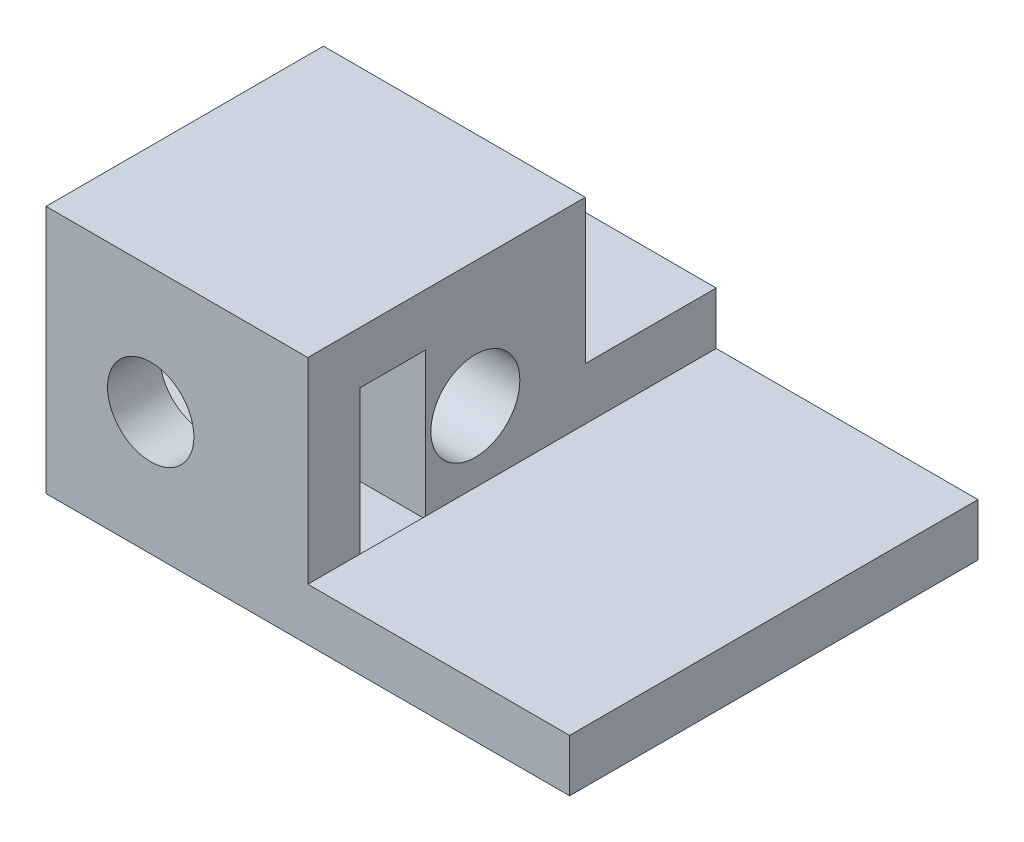
SolidWorks part; units mm, degrees
ref_plane "Plano frontal" through (0, 0, 0) normal (0, 0, 1) x (1, 0, 0)
ref_plane "Plano superior" through (0, 0, 0) normal (0, 1, 0) x (1, 0, 0)
ref_plane "Plano direito" through (0, 0, 0) normal (1, 0, 0) x (0, 0, -1)
sketch "Esboço1" plane through (0, 0, 0) normal (0, 0, 1) x (1, 0, 0)
  line L0 (0, 0) -> (0, 2)
  line L1 (0, 2) -> (5, 2)
  line L2 (5, 2) -> (5, 4)
  line L3 (5, 4) -> (10, 4)
  line L4 (10, 4) -> (10, 2)
  line L5 (20, 0) -> (0, 0)
  line L6 (10, 2) -> (20, 2)
  line L7 (20, 2) -> (20, 0)
  dimension "D1" = 2
  dimension "D2" = 2
  dimension "D3" = 5
  dimension "D4" = 5
  dimension "D5" = 10
extrude "Ressalto-extrusão1" add sketch "Esboço1" along normal mid plane 105
sketch "Esboço3" plane through (0, 0, 52.5) normal (0, 0, 1) x (1, 0, 0)
  line L1 (0, 0) -> (10, 0)
  line L2 (0, 0) -> (0, 4)
  line L3 (0, 4) -> (10, 4)
  line L4 (10, 0) -> (10, 4)
extrude "Ressalto-extrusão2" add sketch "Esboço3" against normal blind 5
sketch "Esboço4" plane through (10, 0, 0) normal (1, 0, 0) x (0, 0, -1)
  line L0 (-52.5, 9.5) -> (-63.1, 9.5)
  line L1 (-52.5, 9.5) -> (-52.5, 3.7429)
  line L2 (-63.1, 0) -> (-52.5, 0)
  line L4 (2.5, 0) -> (2.5, 21.5057) construction
  line L5 (-47.5, 0) -> (52.5, 0) construction
  line L6 (-63.1, 9.5) -> (-63.1, 0)
  line L8 (-61.1, 7.5) -> (-58.6, 7.5)
  line L9 (-52.5, 3.7429) -> (-52.5, 0)
  line L10 (-61.1, 7.5) -> (-61.1, 1.9)
  line L11 (-61.1, 1.9) -> (-58.6, 1.9)
  line L12 (-58.6, 7.5) -> (-58.6, 1.9)
  line L13 (-61.1, 7.5) -> (-58.6, 1.9) construction
  line L14 (-61.1, 1.9) -> (-58.6, 7.5) construction
  circle A0 centre (-56.7, 4.7) radius 1.7
  point P0 (-105, 0)
  point P4 (0, 0)
  point P7 (-106.4656, 8.3439)
  point P14 (-59.85, 4.7)
  point P22 (-116.5265, 8.4)
  point P23 (-109.0163, 8.4)
  point P24 (-115, 3.8609)
  dimension "D1" = 3.4
  dimension "D2" = 2
  dimension "D3" = 2.5
  dimension "D4" = 3
  dimension "D5" = 0.2
  dimension "D6" = 5.6
  dimension "D7" = 2.5
  dimension "D8" = 2
extrude "Ressalto-extrusão3" add sketch "Esboço4" against normal through all
sketch "Esboço5" plane through (0, 0, 63.1) normal (0, 0, 1) x (1, 0, 0)
  line L0 (0, 7.5) -> (0, 1.9) construction
  line L1 (0, 7.5) -> (0, 1.9) construction
  circle A0 centre (4, 4.7) radius 1.65
  point P4 (0, 4.7)
  point P5 (0, 0)
  dimension "D2" = 3.3
  dimension "D1" = 4
extrude "Corte-extrusão1" cut sketch "Esboço5" against normal blind 6
mirror "Espelhar1" about plane through (0, 0, 0) normal (0, 0, 1) of "Corte-extrusão1", "Ressalto-extrusão3"
sketch "Esboço6" plane through (0, 0, 52.5) normal (0, 0, 1) x (1, 0, 0)
  line L4 (10, 2) -> (10, 0)
  line L5 (10, 0) -> (20, 0)
  line L6 (20, 0) -> (20, 2)
  line L7 (20, 2) -> (10, 2)
  line L8 (10, 2) -> (10, 0)
  line L9 (10, 0) -> (20, 0)
  line L10 (20, 0) -> (20, 2)
  line L11 (20, 2) -> (10, 2)
  dimension "D1" = 0
extrude "Ressalto-extrusão4" add sketch "Esboço6" along normal up to surface and the other way up to surface up to face at (5.65, 4.7, 63.1) other way up to face at (5.65, 4.7, -63.1)
sketch "Esboço7" plane through (0, 4, 0) normal (0, 1, 0) x (1, 0, 0)
  line L1 (0, -47.5) -> (20, -47.5)
  line L2 (0, -47.5) -> (0, 63.1)
  line L3 (0, 63.1) -> (20, 63.1)
  line L4 (20, -47.5) -> (20, 63.1)
extrude "Corte-extrusão2" cut sketch "Esboço7" against normal through all both and the other way through all
